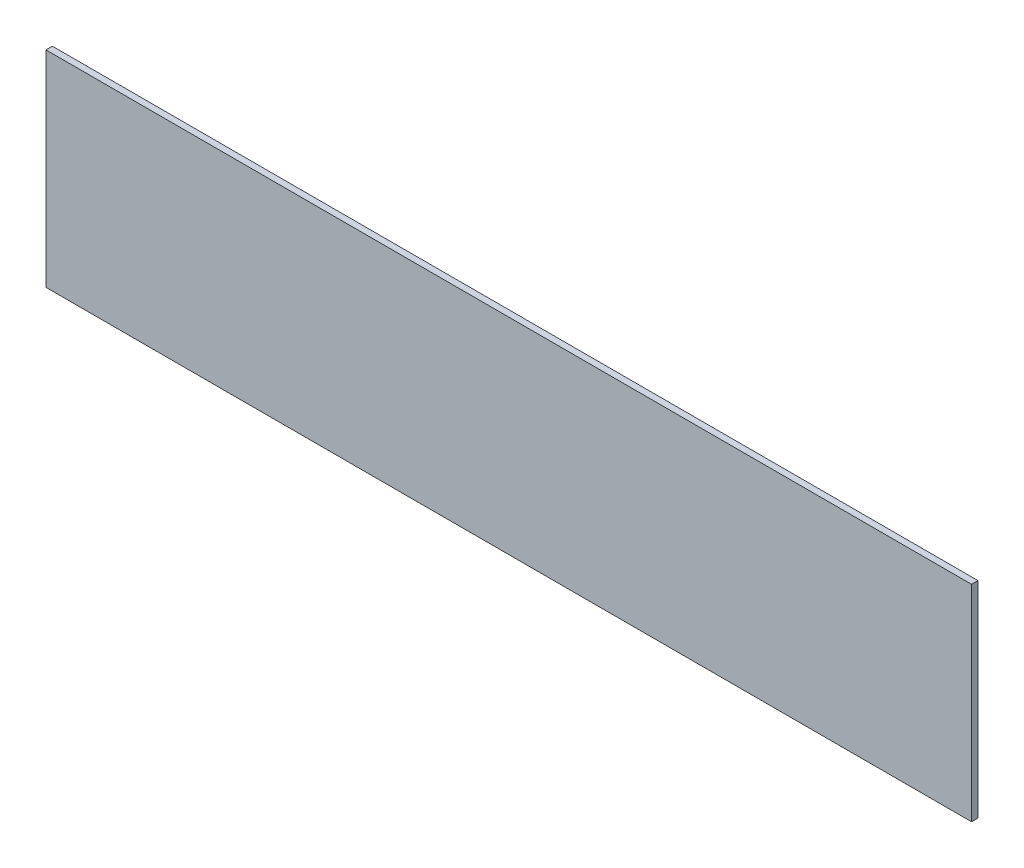
SolidWorks part; units mm, degrees
material "Nylon 101"
ref_plane "Front Plane" through (0, 0, 0) normal (0, 0, 1) x (1, 0, 0)
ref_plane "Top Plane" through (0, 0, 0) normal (0, 1, 0) x (1, 0, 0)
ref_plane "Right Plane" through (0, 0, 0) normal (1, 0, 0) x (0, 0, -1)
sketch "Sketch1" plane through (0, 0, 0) normal (0, 0, 1) x (1, 0, 0)
  line L6 (0, 0) -> (-228.6, 0)
  line L7 (0, 0) -> (0, -50.8)
  line L8 (0, -50.8) -> (-228.6, -50.8)
  line L9 (-228.6, 0) -> (-228.6, -50.8)
  dimension "D1" = 50.8
  dimension "D2" = 228.6
extrude "Boss-Extrude1" add sketch "Sketch1" along normal blind 1.5875
ref_plane "Plane1" through (0, -25.4, 0) normal (0, 1, 0) x (1, 0, 0)
